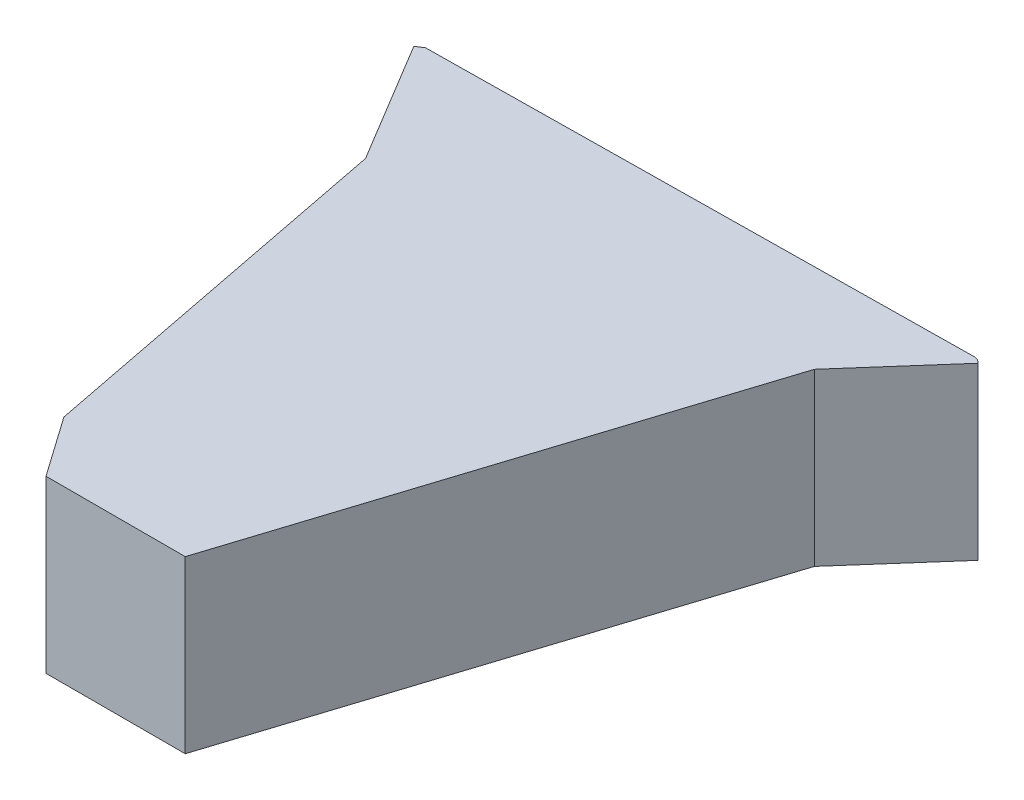
SolidWorks part; units mm, degrees
ref_plane "前视基准面" through (0, 0, 0) normal (0, 0, 1) x (1, 0, 0)
ref_plane "上视基准面" through (0, 0, 0) normal (0, 1, 0) x (1, 0, 0)
ref_plane "右视基准面" through (0, 0, 0) normal (1, 0, 0) x (0, 0, -1)
sketch "草图2" plane through (0, 0, 0) normal (0, 1, 0) x (1, 0, 0)
  line L0 (-180.408, 313.2117) -> (-145.1374, 254.5996)
  line L1 (-147.0329, 253.8705) -> (-111.9274, 73.9045)
  line L2 (-91.5971, 44.9755) -> (-24.728, 44.9755)
  line L3 (48.4282, 273.9688) -> (-24.728, 44.9755)
  line L4 (46.6502, 274.9755) -> (83.7031, 317.1239)
  line L5 (83.7031, 317.1239) -> (85.2052, 315.8034)
  line L6 (85.2052, 315.8034) -> (48.4282, 273.9688)
  line L7 (-26.1886, 46.9755) -> (46.6502, 274.9755)
  line L8 (-26.1886, 46.9755) -> (-90.5581, 46.9755)
  line L10 (-147.0329, 253.8705) -> (-182.1216, 312.1805)
  line L11 (-182.1216, 312.1805) -> (-180.408, 313.2117)
  line L12 (-110.046, 74.7057) -> (-90.5581, 46.9755)
  line L13 (-51.67, 193.4335) -> (-92.281, 169.9867)
  line L14 (-92.281, 169.9867) -> (-92.281, 123.0932)
  line L15 (-92.281, 123.0932) -> (-51.67, 99.6464)
  line L16 (-51.67, 99.6464) -> (-11.059, 123.0932)
  line L17 (-11.059, 123.0932) -> (-11.059, 169.9867)
  line L18 (-11.059, 169.9867) -> (-51.67, 193.4335)
  line L19 (-111.9274, 73.9045) -> (-91.5971, 44.9755)
  line L20 (-110.046, 74.7057) -> (-145.1374, 254.5996)
  circle A0 centre (-100.0036, 94.2573) radius 9
  circle A1 centre (-51.67, 146.54) radius 40.611 construction
  dimension "D1" = 18
  dimension "D2" = 2
  dimension "D3" = 2
  dimension "D4" = 160
  dimension "D5" = 2
  dimension "D7" = 2
  dimension "D9" = 2
  dimension "D10" = 2
extrude "凸台-拉伸1" add sketch "草图2" along normal blind 80
sketch "草图3" plane through (0, 80, 0) normal (0, 1, 0) x (1, 0, 0)
  line L0 (-178.7467, 314.3253) -> (81.7641, 317.6139)
  line L1 (81.7641, 317.6139) -> (83.7031, 317.1239)
  line L2 (-91.5971, 44.9755) -> (-24.728, 44.9755)
  line L3 (-24.728, 44.9755) -> (48.4282, 273.9688)
  line L4 (48.4282, 273.9688) -> (85.2052, 315.8034)
  line L5 (-91.5971, 44.9755) -> (-111.9274, 73.9045)
  line L6 (-180.408, 313.2117) -> (-182.1216, 312.1805)
  line L7 (-182.1216, 312.1805) -> (-147.0329, 253.8705)
  line L8 (-180.408, 313.2117) -> (-178.7467, 314.3253)
  line L10 (85.2052, 315.8034) -> (83.7031, 317.1239)
  line L11 (-111.9274, 73.9045) -> (-91.5971, 44.9755) construction
  line L12 (-147.0329, 253.8705) -> (-111.9274, 73.9045)
extrude "凸台-拉伸2" add sketch "草图3" along normal blind 2
